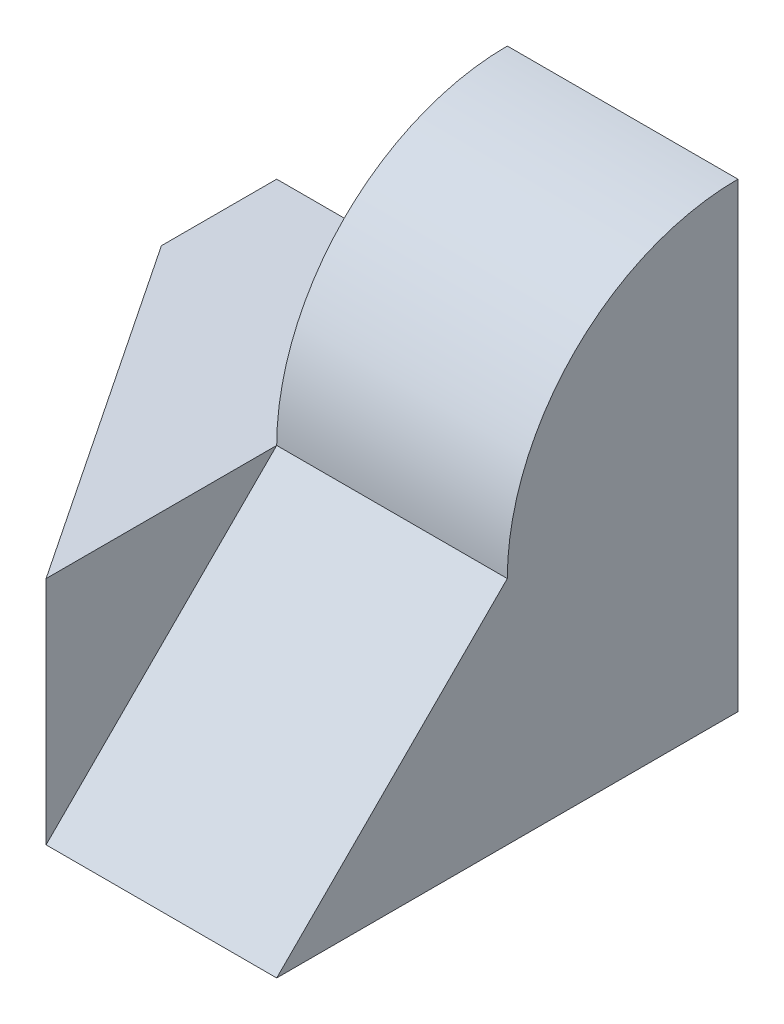
SolidWorks part; units mm, degrees
ref_plane "Front Plane" through (0, 0, 0) normal (0, 0, 1) x (1, 0, 0)
ref_plane "Top Plane" through (0, 0, 0) normal (0, 1, 0) x (1, 0, 0)
ref_plane "Right Plane" through (0, 0, 0) normal (1, 0, 0) x (0, 0, -1)
sketch "Sketch1" plane through (0, 0, 0) normal (0, 0, 1) x (1, 0, 0)
  line L0 (0, 0) -> (0, 40)
  line L1 (0, 40) -> (-20, 40)
  line L2 (-20, 40) -> (-20, 20)
  line L3 (-20, 20) -> (-40, 20)
  line L4 (-40, 20) -> (-40, 0)
  line L5 (-40, 0) -> (0, 0)
  dimension "D1" = 40
  dimension "D2" = 40
  dimension "D3" = 20
  dimension "D4" = 20
extrude "Boss-Extrude1" add sketch "Sketch1" along normal blind 40
sketch "Sketch3" plane through (-20, 0, 0) normal (-1, 0, 0) x (0, 0, 1)
  line L0 (40, 20) -> (0, 20) construction
  line L1 (0, 40) -> (0, 20)
  line L2 (0, 20) -> (20, 20)
  line L3 (0, 40) -> (40, 40)
  line L4 (40, 40) -> (40, 20)
  line L5 (40, 20) -> (20, 20)
  arc A0 (0, 40) -> (20, 20) centre (0, 20) cw
  line M2 (0, 20) -> (40, 20)
  line M3 (40, 20) -> (40, 40)
  line M4 (40, 40) -> (0, 40)
extrude "Cut-Extrude1" cut sketch "Sketch3" against normal blind 40 contours A0 M4 M2 M3
sketch "Sketch5" plane through (0, 20, 0) normal (0, 1, 0) x (1, 0, 0)
  line L0 (-40, 0) -> (-20, 0)
  line L1 (-20, 0) -> (-20, -40)
  line L2 (0, -40) -> (-40, -40) construction
  line L3 (-20, -40) -> (-40, -10)
  line L4 (-40, -40) -> (-40, 0) construction
  line L5 (-40, -10) -> (-40, 0)
  line L6 (-40, -10) -> (-40, -40)
  line L7 (-40, -40) -> (-20, -40)
  line M2 (-40, 0) -> (-40, -40)
  line M3 (-40, -40) -> (0, -40)
  dimension "D1" = 10
extrude "Cut-Extrude2" cut sketch "Sketch5" against normal blind 40 contours L3 M3 M2
sketch "Sketch8" plane through (0, 0, 0) normal (1, 0, 0) x (0, 0, -1)
  line L0 (-20, 20) -> (-40, 0)
  line L1 (-40, 0) -> (-40, 20)
  line L2 (-40, 20) -> (-20, 20)
extrude "Cut-Extrude4" cut sketch "Sketch8" against normal blind 20
